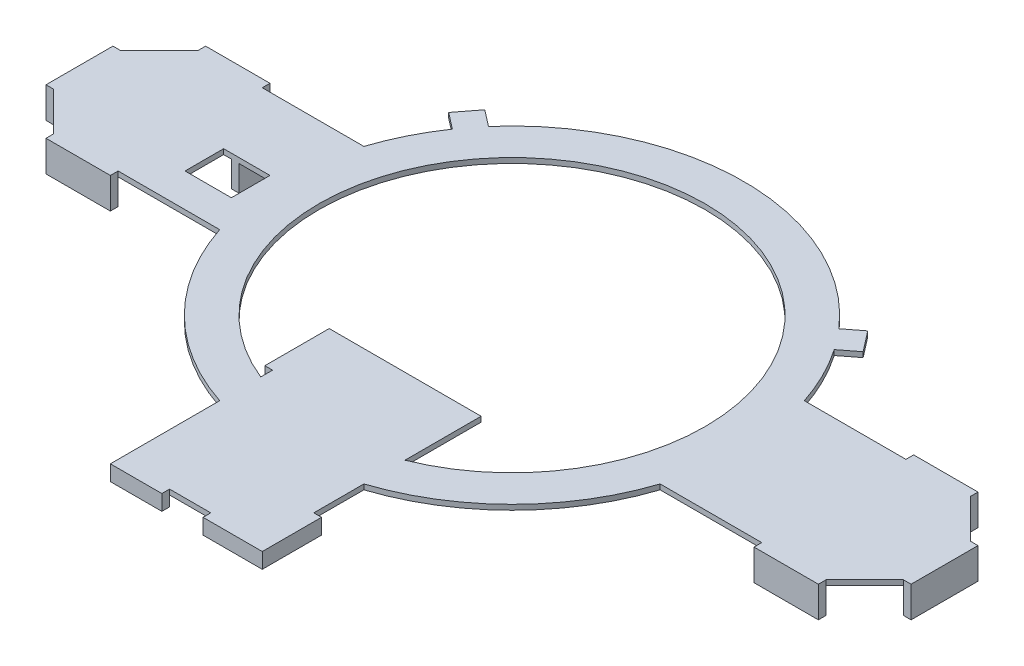
SolidWorks part; units mm, degrees
ref_plane "Front Plane" through (0, 0, 0) normal (0, 0, 1) x (1, 0, 0)
ref_plane "Top Plane" through (0, 0, 0) normal (0, 1, 0) x (1, 0, 0)
ref_plane "Right Plane" through (0, 0, 0) normal (1, 0, 0) x (0, 0, -1)
sketch "Sketch1" plane through (0, 0, 0) normal (0, 1, 0) x (1, 0, 0)
  line L0 (0, -90) -> (0, 90)
  line L5 (-90, 0) -> (90, 0)
  line L6 (-165, 0) -> (165, 0)
  line L7 (-90, -28) -> (90, -28)
  line L8 (-90, -28) -> (-90, 28)
  line L9 (-90, 28) -> (90, 28)
  line L10 (90, -28) -> (90, 28)
  line L11 (-90, -28) -> (-165, -28)
  line L12 (-90, -28) -> (-90, 28)
  line L13 (-90, 28) -> (-165, 28)
  line L14 (-165, -28) -> (-165, 28)
  line L15 (90, -28) -> (165, -28)
  line L16 (90, -28) -> (90, 28)
  line L17 (90, 28) -> (165, 28)
  line L18 (165, -28) -> (165, 28)
  line L19 (-165, 4) -> (-90, 4)
  line L20 (-112, 28) -> (-112, -28)
  line L21 (-165, -15) -> (-90, -15)
  line L22 (-94, -15) -> (-94, 4)
  line L23 (165, -13) -> (165, 13)
  line L24 (-165, -13) -> (-168, -13)
  line L25 (-165, -13) -> (-165, 13)
  line L26 (-165, 13) -> (-168, 13)
  line L27 (-168, -13) -> (-168, 13)
  line L28 (-150, 28) -> (-125, 28)
  line L29 (-150, 28) -> (-150, 31)
  line L30 (-150, 31) -> (-125, 31)
  line L31 (-125, 28) -> (-125, 31)
  line L32 (168, -13) -> (168, 13)
  line L33 (168, -13) -> (165, -13)
  line L34 (168, 13) -> (165, 13)
  line L35 (125, -28) -> (125, -31)
  line L36 (-150, -28) -> (-125, -28)
  line L37 (-150, -28) -> (-150, -31)
  line L38 (-150, -31) -> (-125, -31)
  line L39 (-125, -28) -> (-125, -31)
  line L40 (-112, 13) -> (-109, 13)
  line L41 (-112, 13) -> (-112, 4)
  line L42 (-112, 4) -> (-109, 4)
  line L43 (-109, 13) -> (-109, 4)
  line L44 (125, -28) -> (150, -28)
  line L45 (150, -28) -> (150, -31)
  line L46 (125, -31) -> (150, -31)
  line L47 (125, 28) -> (125, 31)
  line L48 (125, 28) -> (150, 28)
  line L49 (150, 28) -> (150, 31)
  line L50 (125, 31) -> (150, 31)
  line L51 (110, -13) -> (110, 13)
  line L52 (110, -13) -> (107, -13)
  line L53 (107, -13) -> (107, 13)
  line L54 (110, 13) -> (107, 13)
  line L55 (0, -75) -> (0, -90)
  line L56 (0, -90) -> (0, -75)
  line L57 (68.0396, 58.9119) -> (74.1552, 51)
  line L62 (28, -40) -> (-28, -40)
  line L63 (28, -40) -> (28, -125)
  line L64 (28, -125) -> (-28, -125)
  line L65 (-28, -40) -> (-28, -125)
  line L66 (28, -40) -> (-28, -125) construction
  line L67 (28, -125) -> (-28, -40) construction
  line L68 (-28, -125) -> (-8, -125)
  line L69 (-28, -125) -> (-28, -128)
  line L70 (-28, -128) -> (-8, -128)
  line L71 (-8, -125) -> (-8, -128)
  line L76 (28, -125) -> (8, -125)
  line L77 (28, -125) -> (28, -128)
  line L78 (28, -128) -> (8, -128)
  line L79 (8, -125) -> (8, -128)
  line L80 (28, -128) -> (31, -128)
  line L81 (28, -128) -> (28, -105)
  line L82 (28, -105) -> (31, -105)
  line L83 (31, -128) -> (31, -105)
  line L84 (-28, -40) -> (-31, -40)
  line L85 (-28, -40) -> (-28, -65)
  line L86 (-28, -65) -> (-31, -65)
  line L87 (-31, -40) -> (-31, -65)
  line L88 (68.0396, 58.9119) -> (74.3691, 63.8045)
  line L89 (74.1552, 51) -> (80.4848, 55.8925)
  line L90 (74.3691, 63.8045) -> (80.4848, 55.8925)
  line L91 (-74.1552, 51) -> (-80.4848, 55.8925)
  line L92 (-74.3691, 63.8045) -> (-80.4848, 55.8925)
  line L93 (-68.0396, 58.9119) -> (-74.3691, 63.8045)
  line L94 (-68.0396, 58.9119) -> (-74.1552, 51)
  circle A0 centre (0, 0) radius 75
  circle A1 centre (0, 0) radius 90
  circle A2 centre (-90, 0) radius 28
  circle A3 centre (90, 0) radius 28
  point P49 (0, -82.5)
  dimension "D1" = 150
  dimension "D2" = 15
  dimension "D3" = 56
  dimension "D4" = 56
  dimension "D5" = 75
  dimension "D6" = 75
  dimension "D7" = 32
  dimension "D8" = 22
  dimension "D9" = 13
  dimension "D10" = 4
  dimension "D11" = 3
  dimension "D12" = 15
  dimension "D13" = 15
  dimension "D14" = 3
  dimension "D15" = 15
  dimension "D16" = 25
  dimension "D18" = 3
  dimension "D19" = 15
  dimension "D20" = 25
  dimension "D21" = 3
  dimension "D22" = 15
  dimension "D25" = 56
  dimension "D26" = 85
  dimension "D27" = 20
  dimension "D28" = 3
  dimension "D29" = 23
  dimension "D30" = 20
  dimension "D31" = 23
  dimension "D32" = 3
  dimension "D33" = 3
  dimension "D34" = 25
  dimension "D35" = 10
  dimension "D36" = 8
  dimension "D37" = 23
  dimension "D17" = 2
  dimension "D23" = 2
  dimension "D24" = 2
extrude "Boss-Extrude3" add sketch "Sketch1" against normal blind 2 contours A1 A2 A0 L5 | A0 A2 A1 L5 | A2 A1 L7 A0 | L7 A1 L65 A0 | A2 A0 L9 A1 | L0 A1 L94 L9 A0 | A1 L93 L92 L91 | L9 A1 L57 L0 A0 | A1 L89 L90 L88 | A3 A1 L9 A0 | L57 A1 | L94 A1 | A1 A3 A0 L6 | A0 A3 A1 L6 | A3 A0 L7 A1 | L63 A1 L7 A0 | L65 A1 L0 A0 | L0 A1 L63 A0 | A2 L20 L13 L14 L19 | A2 L13 L20 | L13 L31 L30 L29 | A2 L19 L14 L6 | A2 L6 L14 L21 | L27 L24 L14 L26 | L19 A2 L6 L20 | L20 A2 L19 | L6 A2 L21 L20 | L43 L40 L20 L19 | L12 A2 L20 L40 L43 L19 | A1 A2 L12 L8 | L6 L22 L19 L20 | L22 L6 L8 L19 | L22 L21 L12 L6 | A2 L21 L14 L11 L20 | L39 L11 L37 L38 | L21 A2 L20 | L20 A2 L8 L21 | A2 L20 L11 | L8 A2 A1 L12 | A2 L7 A1 | A1 L65 L64 L63 | L71 L64 L69 L70 | L64 L79 L78 L77 | L80 L83 L82 L63 L77 | L65 A0 L0 L62 | L0 A0 L63 L62 | L84 L87 L86 L65 | A1 A3 L10 | L10 A3 A1 | A3 L9 A1 | L6 A3 L10 L53 L54 L51 | A3 L6 L18 L17 | A3 A1 L7 | L10 A3 L6 L51 L52 L53 | A3 L15 L18 L6 | L32 L34 L18 L33 | L35 L46 L45 L15 | L50 L47 L17 L49 | L51 L54 L53 L6 | L53 L52 L51 L6 | A2 A1 L9
sketch "Sketch2" plane through (0, -2, 0) normal (0, -1, 0) x (1, 0, 0)
  line L0 (0, 0) -> (0, -75)
  line L1 (-150, -31) -> (-125, -31)
  line L2 (-150, -31) -> (-150, -28)
  line L3 (-150, -28) -> (-125, -28)
  line L4 (-125, -31) -> (-125, -28)
  line L5 (-165, -13) -> (-168, -13)
  line L6 (-165, -13) -> (-165, 13)
  line L7 (-165, 13) -> (-168, 13)
  line L8 (-168, -13) -> (-168, 13)
  line L9 (-150, 31) -> (-125, 31)
  line L10 (-150, 31) -> (-150, 28)
  line L11 (-150, 28) -> (-125, 28)
  line L12 (-125, 31) -> (-125, 28)
  line L13 (150, -28) -> (125, -28)
  line L14 (125, -31) -> (125, -28)
  line L15 (150, -31) -> (125, -31)
  line L16 (150, -31) -> (150, -28)
  line L17 (165, 13) -> (168, 13)
  line L18 (168, -13) -> (168, 13)
  line L19 (165, -13) -> (168, -13)
  line L20 (165, -13) -> (165, 13)
  line L21 (125, 31) -> (125, 28)
  line L22 (150, 31) -> (125, 31)
  line L23 (150, 31) -> (150, 28)
  line L24 (150, 28) -> (125, 28)
  line L25 (106, 13) -> (109, 13)
  line L26 (109, -13) -> (109, 13)
  line L27 (106, -13) -> (109, -13)
  line L28 (106, -13) -> (106, 13)
  line L29 (-125, -28) -> (-85.5336, -28) construction
  line L30 (-109, -13) -> (-106, -13)
  line L31 (-109, -13) -> (-109, 0)
  line L32 (-109, 0) -> (-106, 0)
  line L33 (-106, -13) -> (-106, 0)
  line L34 (-112, 0) -> (-94, 0) construction
  line L36 (-31, 40) -> (-28, 40)
  line L37 (-31, 40) -> (-31, 65)
  line L38 (-31, 65) -> (-28, 65)
  line L39 (-28, 40) -> (-28, 65)
  line L40 (-28, 128) -> (-8, 128)
  line L41 (-28, 128) -> (-28, 125)
  line L42 (-28, 125) -> (-8, 125)
  line L43 (-8, 128) -> (-8, 125)
  line L44 (31, 128) -> (8, 128)
  line L45 (31, 128) -> (31, 125)
  line L46 (31, 125) -> (8, 125)
  line L47 (8, 128) -> (8, 125)
  line L48 (31, 125) -> (28, 125)
  line L49 (31, 125) -> (31, 105)
  line L50 (31, 105) -> (28, 105)
  line L51 (28, 125) -> (28, 105)
  arc A0 (-28, 69.5773) -> (28, 69.5773) centre (0, 0) ccw construction
  dimension "D2" = 15
  dimension "D3" = 3
  dimension "D4" = 56
  dimension "D5" = 0
  dimension "D1" = 2
extrude "Boss-Extrude4" add sketch "Sketch2" along normal blind 10 contours L24 L23 L22 L21 | L28 L27 L26 L25 | L20 L19 L18 L17 | L15 L16 L13 L14 | L8 L5 L6 L7 | L1 L4 L3 L2 | L30 L33 L32 L31 | L12 L9 L10 L11
sketch "Sketch3" plane through (0, -2, 0) normal (0, -1, 0) x (-1, 0, 0)
  line L1 (28, -65) -> (31, -65)
  line L2 (28, -65) -> (28, -40)
  line L3 (28, -40) -> (31, -40)
  line L4 (31, -65) -> (31, -40)
  line L5 (8, -125) -> (28, -125)
  line L6 (8, -125) -> (8, -128)
  line L7 (8, -128) -> (28, -128)
  line L8 (28, -125) -> (28, -128)
  line L9 (-8, -125) -> (-31, -125)
  line L10 (-8, -125) -> (-8, -128)
  line L11 (-8, -128) -> (-31, -128)
  line L12 (-31, -125) -> (-31, -128)
  line L13 (-28, -105) -> (-31, -105)
  line L14 (-28, -105) -> (-28, -125)
  line L15 (-28, -125) -> (-31, -125)
  line L16 (-31, -105) -> (-31, -125)
extrude "Boss-Extrude5" add sketch "Sketch3" along normal blind 4 contours L1 L4 L3 L2 | L13 L16 L9 L14 | L9 L12 L11 L10 | L7 L8 L5 L6
sketch "Sketch4" plane through (0, -2, 0) normal (0, -1, 0) x (1, 0, 0)
  line L0 (-165, -13) -> (-150, -28)
  line L1 (-165, 13) -> (-150, 28)
  line L2 (150, 28) -> (165, 13)
  line L3 (165, 13) -> (165, -13)
  line L4 (165, -13) -> (150, -28)
  line L5 (150, 28) -> (165, 28)
  line L6 (165, 28) -> (165, 13)
  line L7 (165, -13) -> (165, -28)
  line L8 (165, -28) -> (150, -28)
  line L9 (-150, 28) -> (-165, 28)
  line L10 (-165, 28) -> (-165, 13)
  line L11 (-165, -13) -> (-165, -28)
  line L12 (-165, -28) -> (-150, -28)
extrude "Cut-Extrude1" cut sketch "Sketch4" against normal blind 10 contours L9 L10 L1 | L11 L12 L0 | L6 L5 L2 | L8 L7 L4
